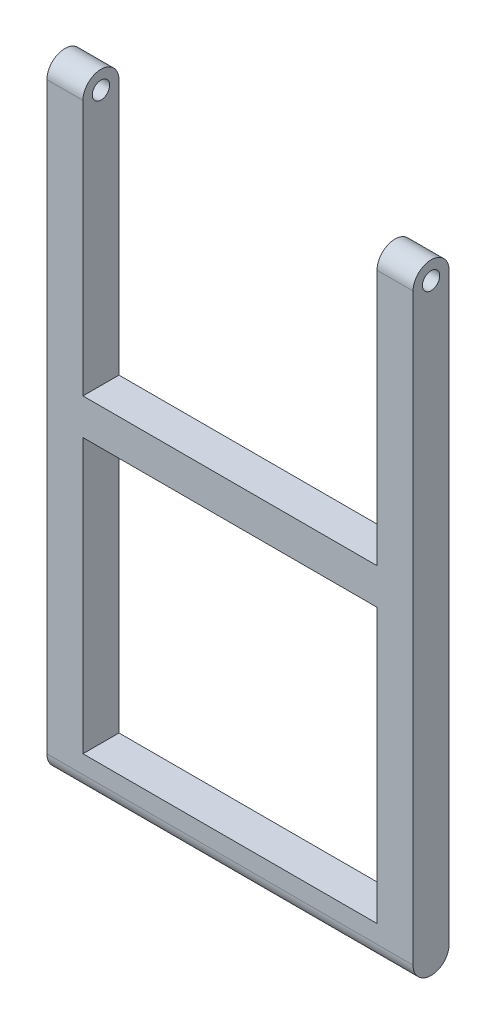
SolidWorks part; units mm, degrees
ref_plane "Přední rovina" through (0, 0, 0) normal (0, 0, 1) x (1, 0, 0)
ref_plane "Horní rovina" through (0, 0, 0) normal (0, 1, 0) x (1, 0, 0)
ref_plane "Pravá rovina" through (0, 0, 0) normal (1, 0, 0) x (0, 0, -1)
sketch "Skica1" plane through (0, 0, 0) normal (0, 0, 1) x (1, 0, 0)
  line L0 (0, 86) -> (0, 0)
  line L1 (0, 0) -> (50.8, 0)
  line L2 (50.8, 0) -> (50.8, 86)
  line L3 (50.8, 86) -> (45.8, 86)
  line L4 (45.8, 86) -> (45.8, 48)
  line L5 (45.8, 48) -> (5, 48)
  line L6 (5, 48) -> (5, 86)
  line L7 (5, 86) -> (0, 86)
  line L9 (5, 43) -> (45.8, 43)
  line L10 (5, 43) -> (5, 5)
  line L11 (5, 5) -> (45.8, 5)
  line L12 (45.8, 43) -> (45.8, 5)
  dimension "D1" = 5
  dimension "D2" = 5
  dimension "D3" = 5
  dimension "D4" = 5
  dimension "D5" = 86
  dimension "D6" = 40.8
  dimension "D7" = 38
extrude "Přidat vysunutím1" add sketch "Skica1" along normal blind 5
sketch "Skica2" plane through (50.8, 0, 0) normal (1, 0, 0) x (0, 0, -1)
  line L0 (-5, 81) -> (0, 81) construction
  line L1 (-5, 0) -> (-5, 86) construction
  line L2 (0, 0) -> (0, 86) construction
  line L3 (0, 81) -> (-5, 86) construction
  line L4 (-5, 86) -> (0, 86) construction
  line L5 (-5, 83.5) -> (-5, 86)
  line L6 (-5, 86) -> (0, 86)
  line L7 (0, 86) -> (0, 83.5)
  circle A0 centre (-2.5, 83.5) radius 1.2
  arc A1 (0, 83.5) -> (-5, 83.5) centre (-2.5, 83.5) ccw
  line M2 (0, 0) -> (0, 86)
  line M3 (0, 86) -> (-5, 86)
  line M4 (-5, 86) -> (-5, 0)
  dimension "D2" = 2.4
  dimension "D1" = 5
extrude "Odebrat vysunutím1" cut sketch "Skica2" against normal through all contours A1 L6 M4 | A1 M2 M3 | A0
sketch "Skica3" plane through (50.8, 0, 0) normal (1, 0, 0) x (0, 0, -1)
  line L0 (-5, 2.5) -> (0, 2.5) construction
  line L1 (-5, 0) -> (-5, 83.5) construction
  line L2 (0, 0) -> (0, 83.5) construction
  line L3 (-5, 0) -> (0, 0) construction
  line L4 (-5, 2.5) -> (-5, 0)
  line L5 (-5, 0) -> (0, 0)
  line L6 (0, 0) -> (0, 2.5)
  arc A0 (-5, 2.5) -> (0, 2.5) centre (-2.5, 2.5) ccw
  line M3 (0, 0) -> (0, 83.5)
  line M5 (-5, 83.5) -> (-5, 0)
  line M6 (-5, 0) -> (0, 0)
extrude "Odebrat vysunutím2" cut sketch "Skica3" against normal through all contours A0 M5 M6 | A0 L5 M3
